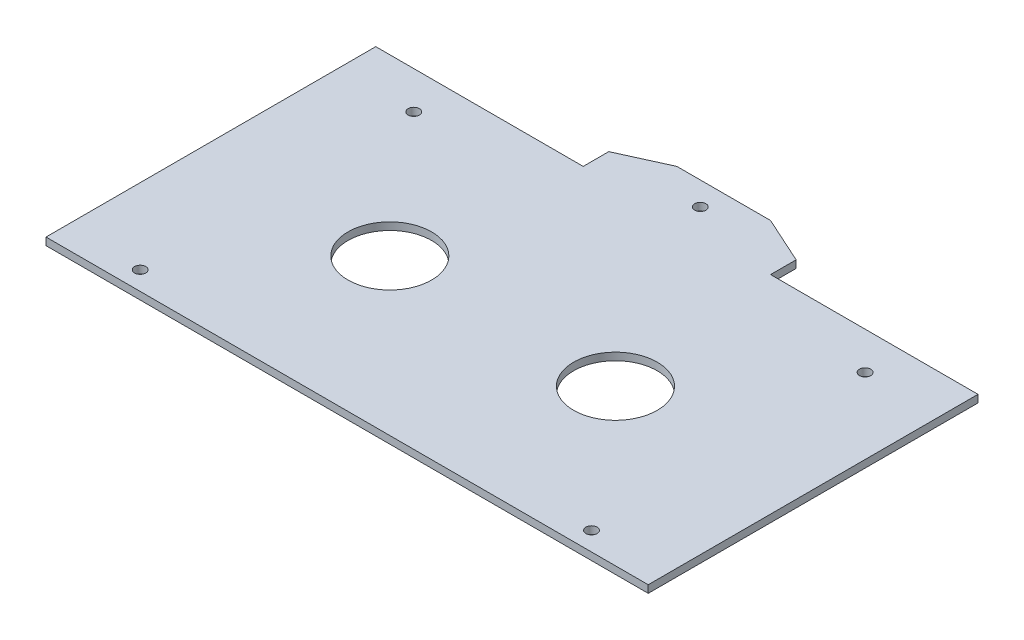
SolidWorks part; units mm, degrees
ref_plane "Front Plane" through (0, 0, 0) normal (0, 0, 1) x (1, 0, 0)
ref_plane "Top Plane" through (0, 0, 0) normal (0, 1, 0) x (1, 0, 0)
ref_plane "Right Plane" through (0, 0, 0) normal (1, 0, 0) x (0, 0, -1)
sketch "Sketch1" plane through (0, 0, 0) normal (0, 1, 0) x (1, 0, 0)
  line L0 (-60.5421, -44) -> (-57.5421, -44)
  line L1 (79.0231, -44) -> (79.0231, -34)
  line L2 (79.0231, -34) -> (-76.6797, -34)
  line L3 (-76.6797, -34) -> (-76.6797, -44)
  line L4 (-76.6797, 24) -> (79.0231, 24)
  line L5 (79.0231, 24) -> (79.0231, 44)
  line L6 (62.8855, 44) -> (59.8855, 44)
  line L7 (-76.6797, 44) -> (-76.6797, 24)
  line L8 (-76.6797, 44) -> (-76.6797, -44)
  line L9 (-60.5421, 44) -> (-57.5421, 44)
  line L10 (-60.5421, -44) -> (-57.5421, -44)
  line L11 (79.0231, 44) -> (79.0231, -44)
  line L12 (-76.6797, 34) -> (79.0231, 34) construction
  line L13 (62.8855, 44) -> (59.8855, 44)
  line L14 (59.8855, -44) -> (62.8855, -44)
  line L15 (-60.5421, -44) -> (-57.5421, -44)
  line L16 (-57.5421, 44) -> (-60.5421, 44)
  line L17 (-76.6797, -39) -> (79.0231, -39) construction
  line L18 (-57.5421, 44) -> (-60.5421, 44)
  line L19 (59.8855, 44) -> (62.8855, 44)
  line L20 (59.8855, -44) -> (62.8855, -44)
  line L21 (59.8855, -44) -> (62.8855, -44)
  line L22 (-59.0421, 44) -> (-59.0421, 24) construction
  line L23 (61.3855, 44) -> (61.3855, 24) construction
  line L24 (61.3855, -44) -> (61.3855, -34) construction
  line L25 (-59.0421, -44) -> (-59.0421, -34) construction
  line L26 (-76.6797, 24) -> (79.0231, 24)
  line L27 (79.0231, 24) -> (79.0231, 44)
  line L28 (79.0231, 44) -> (-76.6797, 44)
  line L29 (-76.6797, 44) -> (-76.6797, 24)
  line L30 (-76.6797, -44) -> (79.0231, -44)
  circle A0 centre (-59.0421, -39) radius 1.5
  circle A1 centre (61.3855, -39) radius 1.5
  circle A2 centre (61.3855, 34) radius 1.5
  circle A3 centre (-59.0421, 34) radius 1.5
  dimension "D1" = 3
extrude "Boss-Extrude2" add sketch "Sketch1" along normal blind 2 contours L11 L4 L8 L2 | L5 L28 L6 L9 L7 L4 A3 A2 | L3 L30 L0 L14 L1 L2 A1 A0
sketch "Sketch2" plane through (0, 2, 0) normal (0, 1, 0) x (1, 0, 0)
  line L0 (79.0231, 44) -> (79.0231, -44)
  line L1 (79.0231, 44) -> (84.0231, 44)
  line L2 (79.0231, -44) -> (84.0231, -44)
  line L3 (84.0231, 44) -> (84.0231, -44)
  line L4 (-76.6797, 44) -> (-76.6797, -44)
  line L5 (-76.6797, 44) -> (-81.6797, 44)
  line L6 (-76.6797, -44) -> (-81.6797, -44)
  line L7 (-81.6797, 44) -> (-81.6797, -44)
  dimension "D1" = 5
  dimension "D2" = 5
extrude "Boss-Extrude3" add sketch "Sketch2" against normal up to surface (2 mm away) up to face at (1.1717, 0, 0)
sketch "Sketch3" plane through (0, 2, 0) normal (0, 1, 0) x (1, 0, 0)
  line L0 (-59.0421, 34) -> (-59.0421, -39) construction
  line L1 (-59.0421, -39) -> (61.3855, -39) construction
  line L2 (61.3855, -39) -> (61.3855, 34) construction
  line L3 (61.3855, 34) -> (-59.0421, 34) construction
  line L4 (-59.0421, -2.5) -> (1.1717, -2.5) construction
  line L5 (1.1717, 34) -> (1.1717, -39) construction
  line L6 (1.1717, -2.5) -> (61.3855, -2.5) construction
  circle A0 centre (-28.9352, -2.5) radius 11.15
  circle A1 centre (31.2786, -2.5) radius 11.15
  dimension "D1" = 22.3
  dimension "D2" = 22.3
extrude "Cut-Extrude1" cut sketch "Sketch3" against normal blind 10
sketch "Sketch4" plane through (0, 2, 0) normal (0, 1, 0) x (1, 0, 0)
  line L0 (-23.8283, 44) -> (26.1717, 44)
  line L1 (26.1717, 44) -> (26.1717, 50.8236)
  line L2 (26.1717, 50.8236) -> (13.6717, 56.4949)
  line L3 (13.6717, 56.4949) -> (-11.3283, 56.4949)
  line L4 (-11.3283, 56.4949) -> (-23.8283, 50.8236)
  line L5 (-23.8283, 50.8236) -> (-23.8283, 44)
  line L6 (1.1717, 56.4949) -> (1.1717, 44) construction
  line L7 (84.0231, 44) -> (-81.6797, 44) construction
  circle A0 centre (1.1717, 50.2475) radius 1.5
  point P0 (1.1717, 44)
  point P11 (1.1717, 44)
  dimension "D1" = 3
extrude "Boss-Extrude4" add sketch "Sketch4" against normal up to surface (2 mm away) up to face at (-28.9352, 0, 13.65)
sketch "Sketch7" plane through (0, 2, 0) normal (0, 1, 0) x (1, 0, 0)
  line L0 (-81.6797, 44) -> (-81.6797, -44)
  line L1 (-81.6797, 44) -> (-80.1797, 44)
  line L2 (-81.6797, -44) -> (-80.1797, -44)
  line L3 (-80.1797, 44) -> (-80.1797, -44)
  line L4 (84.0231, 44) -> (82.5231, 44)
  line L5 (84.0231, 44) -> (84.0231, -43.8521)
  line L6 (82.5231, 44) -> (82.5231, -43.8521)
  line L7 (84.0231, -43.8521) -> (82.5231, -43.8521)
  line L8 (84.0231, 44) -> (26.1717, 44) construction
  dimension "D1" = 1.5
  dimension "D2" = 1.5
extrude "Cut-Extrude2" cut sketch "Sketch7" against normal blind 10
sketch "Sketch8" plane through (0, 2, 0) normal (0, 1, 0) x (1, 0, 0)
  line L0 (-80.1797, 44) -> (-80.1797, -50.0047)
  line L1 (-80.1797, 44) -> (-79.1797, 44)
  line L2 (-80.1797, -50.0047) -> (-79.1797, -50.0047)
  line L3 (-79.1797, 44) -> (-79.1797, -50.0047)
  line L4 (82.5231, 44) -> (82.5231, -58.0122)
  line L5 (82.5231, 44) -> (81.5231, 44)
  line L6 (82.5231, -58.0122) -> (81.5231, -58.0122)
  line L7 (81.5231, 44) -> (81.5231, -58.0122)
  line L8 (84.0231, -43.8521) -> (84.0231, -44)
  line L9 (84.0231, -43.8521) -> (82.1591, -43.8521)
  line L10 (84.0231, -44) -> (82.1591, -44)
  line L11 (82.1591, -43.8521) -> (82.1591, -44)
  line M2 (-80.1797, 44) -> (-80.1797, -44)
  line M3 (-80.1797, -44) -> (84.0231, -44)
  line M4 (84.0231, -44) -> (84.0231, -43.8521)
  line M5 (84.0231, -43.8521) -> (82.5231, -43.8521)
  line M6 (82.5231, -43.8521) -> (82.5231, 44)
  line M7 (82.5231, 44) -> (26.1717, 44)
  line M13 (-23.8283, 44) -> (-80.1797, 44)
  dimension "D1" = 1
  dimension "D2" = 1
extrude "Cut-Extrude5" cut sketch "Sketch8" against normal blind 66.5 contours L9 L11 L4 M3 | L4 M5 M3 M4 | L11 L9 L7 M6 M7 M3 | L3 M13 M2 M3
